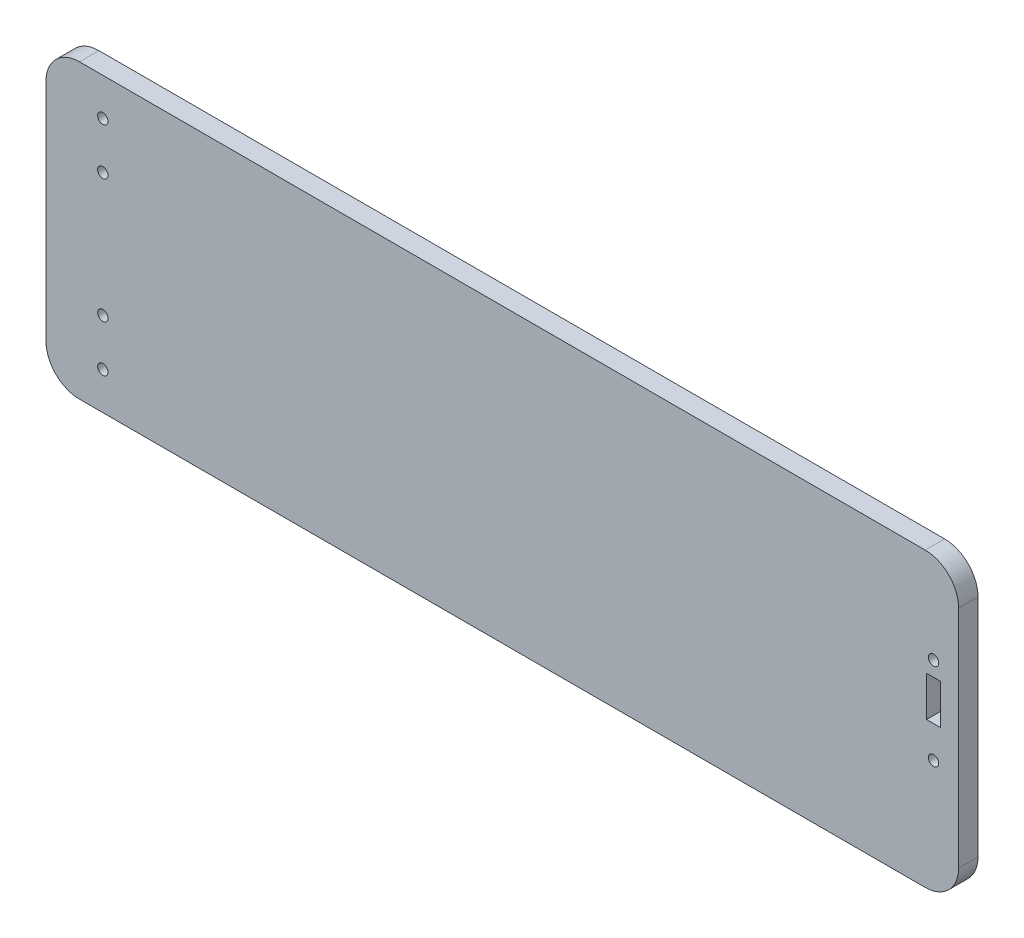
SolidWorks part; units mm, degrees
material "Acrylic (Medium-high impact)"
ref_plane "Front" through (0, 0, 0) normal (0, 0, 1) x (1, 0, 0)
ref_plane "Top" through (0, 0, 0) normal (0, 1, 0) x (1, 0, 0)
ref_plane "Right" through (0, 0, 0) normal (1, 0, 0) x (0, 0, -1)
sketch "Sketch2" plane through (0, 0, 0) normal (0, 0, 1) x (1, 0, 0)
  line L4 (263, 43.7) -> (10, 43.7)
  line L5 (0, 33.7) -> (0, -33.7)
  line L6 (263, -43.7) -> (10, -43.7)
  line L7 (273, 33.7) -> (273, -33.7)
  arc A4 (10, 43.7) -> (0, 33.7) centre (10, 33.7) ccw
  arc A5 (0, -33.7) -> (10, -43.7) centre (10, -33.7) ccw
  arc A6 (263, -43.7) -> (273, -33.7) centre (263, -33.7) ccw
  arc A7 (273, 33.7) -> (263, 43.7) centre (263, 33.7) ccw
  point P5 (273, 0)
  dimension "D3" = 10
  dimension "D1" = 273
  dimension "D2" = 87.4
extrude "Boss-Extrude1" add sketch "Sketch2" along normal blind 5.8
sketch "Sketch3" plane through (0, 0, 5.8) normal (0, 0, 1) x (1, 0, 0)
  line L0 (0, 33.7) -> (0, -33.7) construction
  line L1 (267.6, 0) -> (263.4, 0)
  line L2 (267.6, 0) -> (267.6, 12)
  line L3 (267.6, 12) -> (263.4, 12)
  line L4 (263.4, 0) -> (263.4, 12)
  point P7 (265.5, 12)
  dimension "D1" = 4.2
  dimension "D2" = 12
  dimension "D3" = 265.5
extrude "Cut-Extrude1" cut sketch "Sketch3" against normal blind 6.35
sketch "Sketch4" plane through (0, 0, 5.8) normal (0, 0, 1) x (1, 0, 0)
  line L0 (0, 0) -> (273, 0) construction
  line L1 (0, 33.7) -> (0, -33.7) construction
  line L2 (273, -33.7) -> (273, 33.7) construction
  line L3 (17, 32.5) -> (17, 18.5) construction
  line L4 (17, -32.5) -> (17, -18.5) construction
  line L5 (17, 32.5) -> (17, 18.5) construction
  circle A0 centre (17, 32.5) radius 1.55
  circle A1 centre (17, 18.5) radius 1.55
  circle A2 centre (17, -18.5) radius 1.55
  circle A3 centre (17, -32.5) radius 1.55
  point P14 (17, 25.5)
  dimension "D1" = 3.1
  dimension "D2" = 17
  dimension "D3" = 25.5
  dimension "D4" = 14
extrude "Cut-Extrude2" cut sketch "Sketch4" against normal through all
sketch "Sketch5" plane through (0, 0, 5.8) normal (0, 0, 1) x (1, 0, 0)
  line L0 (267.6, 12) -> (263.4, 12) construction
  line L1 (263.4, 0) -> (267.6, 0) construction
  circle A0 centre (265.5, 16.45) radius 1.55
  circle A1 centre (265.5, -9.55) radius 1.55
  point P9 (265.5, 12)
  dimension "D1" = 3.1
  dimension "D2" = 4.45
  dimension "D3" = 9.55
extrude "Cut-Extrude3" cut sketch "Sketch5" against normal through all
